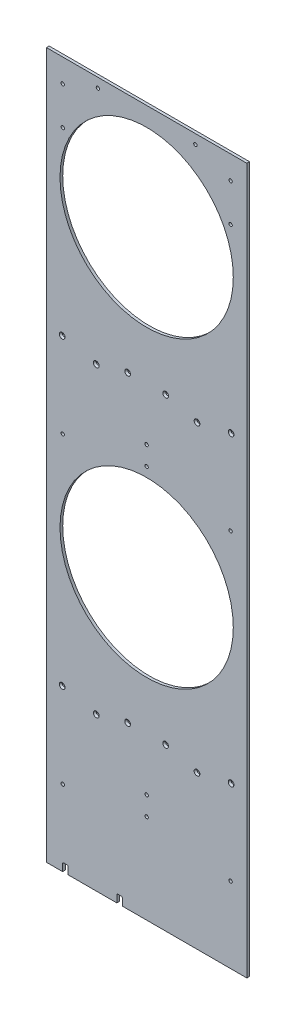
SolidWorks part; units mm, degrees
material "PC High Viscosity"
ref_plane "Front Plane" through (0, 0, 0) normal (0, 0, 1) x (1, 0, 0)
ref_plane "Top Plane" through (0, 0, 0) normal (0, 1, 0) x (1, 0, 0)
ref_plane "Right Plane" through (0, 0, 0) normal (1, 0, 0) x (0, 0, -1)
sketch "Sketch1" plane through (0, 0, 0) normal (0, 0, 1) x (1, 0, 0)
  line L0 (0, 695.96) -> (0, 1407.16) construction
  line L1 (-234.95, 0) -> (234.95, 0)
  line L2 (-234.95, 0) -> (-234.95, 2413)
  line L3 (-234.95, 2413) -> (234.95, 2413)
  line L4 (234.95, 0) -> (234.95, 2413)
  circle A0 centre (0, 695.96) radius 203.2
  circle A1 centre (0, 1407.16) radius 203.2
  circle A2 centre (0, 2118.36) radius 203.2
  dimension "D3" = 406.4
  dimension "D1" = 2413
  dimension "D2" = 469.9
  dimension "D4" = 492.76
  dimension "D6" = 711.2
  dimension "D5" = 3
extrude "Boss-Extrude1" add sketch "Sketch1" along normal blind 6.35
hole_wizard "CSK for 1/4 Flat Head Socket Cap Screw1" positions "Sketch2" profile "Sketch3" countersink size "1/4" standard "ANSI Inch"
sketch "Sketch2" plane through (0, 0, 6.35) normal (0, 0, 1) x (1, 0, 0)
  line L0 (0, 0) -> (0, 2413) construction
  line L1 (234.95, 2413) -> (-234.95, 2413) construction
  line L3 (2.839, 370.0053) -> (12.7, 406.807) construction
  line L4 (2.839, 370.0053) -> (225.089, 310.4536) construction
  line L5 (12.7, 406.807) -> (234.95, 347.2553) construction
  line L6 (225.089, 310.4536) -> (234.95, 347.2553) construction
  line L7 (234.95, 0) -> (234.95, 2413) construction
  line L8 (-234.95, 0) -> (234.95, 0) construction
  line L9 (7.7695, 388.4062) -> (230.0195, 328.8545) construction
  line L11 (118.1748, 358.8231) -> (118.1748, 1070.0231) construction
  line L12 (12.7, 406.807) -> (0, 410.21) construction
  line L14 (12.7, 406.807) -> (14.3435, 412.9407) construction
  line L15 (12.7, 406.807) -> (233.3065, 347.6957) construction
  line L16 (14.3435, 412.9407) -> (234.95, 353.8293) construction
  line L17 (233.3065, 347.6957) -> (234.95, 353.8293) construction
  circle A0 centre (198.12, 376.8459) radius 6.35 construction
  point P0 (44.5713, 378.5452)
  point P2 (118.1748, 358.8231)
  point P4 (-44.5713, 378.5452)
  point P6 (-118.1748, 358.8231)
  point P187 (44.5713, 1089.7452)
  point P188 (118.1748, 1070.0231)
  point P189 (-44.5713, 1089.7452)
  point P190 (-118.1748, 1070.0231)
  point P191 (44.5713, 1800.9452)
  point P192 (118.1748, 1781.2231)
  point P193 (-44.5713, 1800.9452)
  point P194 (-118.1748, 1781.2231)
  point P380 (198.12, 376.8459)
  point P382 (-198.12, 376.8459)
  point P386 (-198.12, 1088.0459)
  point P387 (-198.12, 1799.2459)
  point P388 (198.12, 1799.2459)
  point P389 (198.12, 1088.0459)
  point P453 (114.3, 968.375) [skipped]
  point P454 (114.3, 923.925) [skipped]
  dimension "D10" = 12.7
  dimension "D11" = 6.35
  dimension "D1" = 38.1
  dimension "D2" = 410.21
  dimension "D3" = 15
  dimension "D4" = 38.1
  dimension "D5" = 114.3
  dimension "D7" = 711.2
  dimension "D8" = 12.7
  dimension "D9" = 6.35
  dimension "D12" = 186.8565
  dimension "D13" = 198.12
  dimension "D6" = 3
sketch "Sketch3" plane through (44.5713, 378.5452, 6.35) normal (1, 0, 0) x (0, -1, 0)
  line L0 (0, 0) -> (0, 6.35)
  line L1 (0, 6.35) -> (3.3782, 6.35)
  line L2 (3.3782, 6.35) -> (3.3782, 3.8716)
  line L3 (3.3782, 3.8716) -> (6.7437, 0)
  line L5 (6.7437, 0) -> (0, 0)
  line L6 (-3.3782, 3.8716) -> (-6.7437, 0) construction
  line L11 (0, -6.35) -> (0, 107.95) construction
  dimension "Thru Hole Dia." = 6.7564
  dimension "Thru Hole Depth" = 6.35
  dimension "Near C'Sink Dia." = 13.4874
  dimension "Near C'Sink Angle" = 82
hole_wizard "5/16 (0.3125) Diameter Hole1" positions "Sketch4" profile "Sketch5" hole size "5/16" standard "ANSI Inch" end condition through all
sketch "Sketch4" plane through (0, 0, 6.35) normal (0, 0, 1) x (1, 0, 0)
  line L0 (0, 0) -> (0, 2413) construction
  line L1 (234.95, 2413) -> (-234.95, 2413) construction
  line L3 (-234.95, 232.41) -> (0, 232.41) construction
  line L5 (0, 254.635) -> (0, 210.185) construction
  line L7 (-234.95, 2413) -> (-234.95, 0) construction
  line L8 (-234.95, 0) -> (234.95, 0) construction
  line L9 (196.85, 889) -> (196.85, 1600.2) construction
  line L10 (-114.3, 1677.035) -> (-114.3, 1632.585) construction
  line L12 (-114.3, 1654.81) -> (0, 1654.81) construction
  point P0 (0, 254.635)
  point P2 (0, 210.185)
  point P4 (-196.85, 177.8)
  point P27 (196.85, 177.8)
  point P41 (0, 965.835)
  point P42 (0, 921.385)
  point P43 (-196.85, 889)
  point P44 (196.85, 889)
  point P74 (-196.85, 1600.2)
  point P75 (196.85, 1600.2)
  point P78 (-114.3, 1632.585)
  point P80 (-114.3, 1677.035)
  point P82 (114.3, 1677.035)
  point P84 (114.3, 1632.585)
  point P100 (196.85, 1511.3)
  point P103 (-196.85, 1511.3)
  dimension "D1" = 711.2
  dimension "D2" = 44.45
  dimension "D3" = 38.1
  dimension "D4" = 177.8
  dimension "D5" = 232.41
  dimension "D7" = 2
  dimension "D8" = 711.2
  dimension "D9" = 711.2
  dimension "D10" = 44.45
  dimension "D11" = 228.6
  dimension "D12" = 1511.3
  dimension "D6" = 2
sketch "Sketch5" plane through (0, 254.635, 6.35) normal (1, 0, 0) x (0, -1, 0)
  line L0 (0, 0) -> (0, 6.35)
  line L1 (0, 6.35) -> (3.9687, 6.35)
  line L2 (3.9687, 6.35) -> (3.9687, 0)
  line L5 (3.9687, 0) -> (0, 0)
  line L11 (0, -6.35) -> (0, 107.95) construction
  dimension "Thru Hole Dia." = 7.9375
  dimension "Thru Hole Depth" = 6.35
sketch "Sketch6" plane through (0, 0, 6.35) normal (0, 0, 1) x (1, 0, 0)
  line L0 (234.95, 0) -> (234.95, 2413) construction
  line L1 (-234.95, 2413) -> (234.95, 2413)
  line L2 (-234.95, 2413) -> (-234.95, 1654.81)
  line L3 (-234.95, 1654.81) -> (234.95, 1654.81)
  line L4 (234.95, 2413) -> (234.95, 1654.81)
  line L5 (114.3, 1632.585) -> (114.3, 1677.035) construction
  point P11 (114.3, 1654.81)
extrude "Cut-Extrude1" cut sketch "Sketch6" against normal through all
sketch "Sketch7" [suppressed] plane through (0, 0, 6.35) normal (0, 0, 1) x (1, 0, 0)
  line L0 (234.95, 0) -> (234.95, 1654.81) construction
  line L1 (-234.95, 0) -> (234.95, 0)
  line L2 (-234.95, 0) -> (-234.95, -8.89)
  line L3 (-234.95, -8.89) -> (234.95, -8.89)
  line L4 (234.95, 0) -> (234.95, -8.89)
  dimension "D1" = 8.89
extrude "Boss-Extrude2" [suppressed] add sketch "Sketch7" against normal up to surface (6.35 mm away)
sketch "Sketch8" plane through (0, 0, 6.35) normal (0, 0, 1) x (1, 0, 0)
  line L0 (-234.95, 0) -> (234.95, 0) construction
  line L1 (-183.896, 0) -> (-197.104, 0)
  line L2 (-183.896, 0) -> (-183.896, 19.05)
  line L3 (-183.896, 19.05) -> (-197.104, 19.05)
  line L4 (-197.104, 0) -> (-197.104, 19.05)
  line L6 (-70.104, 0) -> (-56.896, 0)
  line L7 (-70.104, 0) -> (-70.104, 19.05)
  line L8 (-70.104, 19.05) -> (-56.896, 19.05)
  line L9 (-56.896, 0) -> (-56.896, 19.05)
  point P10 (-63.5, 0)
  point P11 (-190.5, 0)
  line M34 (-234.95, 0) -> (234.95, 0)
  dimension "D1" = 63.5
  dimension "D2" = 127
  dimension "D3" = 19.05
  dimension "D4" = 13.208
extrude "Cut-Extrude2" cut sketch "Sketch8" against normal through all contours L9 L8 L7 M34 | L4 L2 L3 M34
fillet "Fillet1" radius 3.175 4 edges at (-183.896, 19.05, 3.175) (-197.104, 19.05, 3.175) (-56.896, 19.05, 3.175) (-70.104, 19.05, 3.175)
